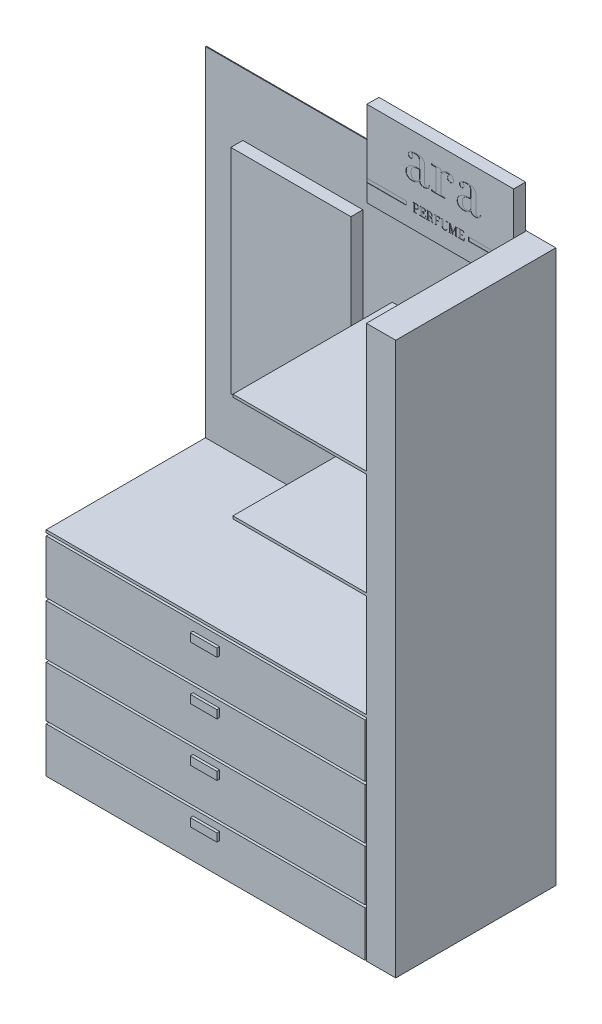
SolidWorks part; units mm, degrees
ref_plane "Front Plane" through (0, 0, 0) normal (0, 0, 1) x (1, 0, 0)
ref_plane "Top Plane" through (0, 0, 0) normal (0, 1, 0) x (1, 0, 0)
ref_plane "Right Plane" through (0, 0, 0) normal (1, 0, 0) x (0, 0, -1)
sketch "Sketch1" plane through (0, 0, 0) normal (0, 0, 1) x (1, 0, 0)
  line L1 (-655, 1035) -> (655, 1035)
  line L2 (-655, 1035) -> (-655, -1035)
  line L3 (-655, -1035) -> (655, -1035)
  line L4 (655, 1035) -> (655, -1035)
  line L5 (-655, 1035) -> (655, -1035) construction
  line L6 (-655, -1035) -> (655, 1035) construction
  point P0 (0, 0)
  dimension "D1" = 1310
  dimension "D2" = 2070
extrude "Boss-Extrude1" add sketch "Sketch1" along normal blind 600
sketch "Sketch2" plane through (0, 0, 600) normal (0, 0, 1) x (1, 0, 0)
  line L0 (-655, -1035) -> (655, -1035) construction
  line L1 (545, -235) -> (-655, -235)
  line L2 (545, -235) -> (545, 165)
  line L3 (545, 165) -> (-655, 165)
  line L4 (-655, -235) -> (-655, 165)
  line L6 (-655, 1035) -> (-655, -1035) construction
  dimension "D1" = 400
  dimension "D2" = 1200
  dimension "D3" = 800
extrude "Cut-Extrude2" cut sketch "Sketch2" against normal offset from surface (597 mm away) 3 up to face at (0, 0, 0)
sketch "Sketch5" plane through (0, 0, 600) normal (0, 0, 1) x (1, 0, 0)
  line L8 (545, -245) -> (-655, -245)
  line L9 (545, -245) -> (545, -255)
  line L10 (545, -255) -> (-655, -255)
  line L11 (-655, -245) -> (-655, -255)
  line L12 (-655, 1035) -> (-655, 165) construction
  line L13 (545, -235) -> (-655, -235) construction
  line L14 (655, -1035) -> (655, 1035) construction
  dimension "D1" = 10
  dimension "D2" = 10
  dimension "D3" = 110
extrude "Cut-Extrude5" cut sketch "Sketch5" against normal offset from surface (597 mm away) 3 up to face at (0, 0, 0)
sketch "Sketch6" plane through (0, 0, 600) normal (0, 0, 1) x (1, 0, 0)
  line L1 (545, -455) -> (-655, -455)
  line L2 (545, -455) -> (545, -465)
  line L3 (545, -465) -> (-655, -465)
  line L4 (-655, -455) -> (-655, -465)
  line L5 (-655, -255) -> (-655, -1035) construction
  line L6 (-655, -255) -> (545, -255) construction
  line L7 (655, -1035) -> (655, 1035) construction
  dimension "D1" = 10
  dimension "D2" = 200
  dimension "D3" = 110
extrude "Cut-Extrude6" cut sketch "Sketch6" against normal offset from surface (597 mm away) 3 up to face at (0, 0, 0)
pattern_linear "LPattern2" count 3 spacing 200 along (0, -1, 0) of "Cut-Extrude6"
sketch "Sketch9" plane through (0, 0, 600) normal (0, 0, 1) x (1, 0, 0)
  line L0 (545, -255) -> (-655, -255) construction
  line L1 (-105, -289.2371) -> (-5, -289.2371)
  line L2 (-105, -289.2371) -> (-105, -319.2371)
  line L3 (-105, -319.2371) -> (-5, -319.2371)
  line L4 (-5, -289.2371) -> (-5, -319.2371)
  point P6 (-55, -255)
  point P7 (-55, -289.2371)
  dimension "D1" = 100
  dimension "D2" = 30
extrude "Boss-Extrude2" add sketch "Sketch9" along normal blind 10
pattern_linear "LPattern3" count 4 spacing 200 along (0, -1, 0) of "Boss-Extrude2"
sketch "Sketch11" plane through (0, 0, 600) normal (0, 0, 1) x (1, 0, 0)
  line L0 (655, 1035) -> (-655, 1035) construction
  line L1 (655, -1035) -> (545, -1035)
  line L2 (655, -1035) -> (655, 1035)
  line L3 (655, 1035) -> (545, 1035)
  line L4 (545, -1035) -> (545, 1035)
  dimension "D1" = 110
extrude "Boss-Extrude3" add sketch "Sketch11" against normal up to surface (600 mm away) separate body up to face at (0, 0, 0)
sketch "Sketch12" plane through (0, 0, 600) normal (0, 0, 1) x (1, 0, 0)
  line L0 (545, 1035) -> (545, -1035) construction
  line L1 (545, 665) -> (45, 665)
  line L2 (545, 665) -> (545, 675)
  line L3 (545, 675) -> (45, 675)
  line L4 (45, 665) -> (45, 675)
  line L6 (545, 165) -> (-655, 165) construction
  dimension "D1" = 10
  dimension "D2" = 500
  dimension "D3" = 500
extrude "Cut-Extrude9" cut sketch "Sketch12" against normal offset from surface (597 mm away) 3 up to face at (0, 0, 0)
sketch "Sketch13" plane through (0, 0, 600) normal (0, 0, 1) x (1, 0, 0)
  line L1 (545, 165) -> (-655, 165)
  line L2 (545, 165) -> (545, 1035)
  line L3 (545, 1035) -> (-655, 1035)
  line L4 (-655, 165) -> (-655, 1035)
extrude "Cut-Extrude10" cut sketch "Sketch13" against normal offset from surface (597 mm away) 3 up to face at (0, 0, 0)
sketch "Sketch14" plane through (0, 0, 3) normal (0, 0, 1) x (1, 0, 0)
  line L0 (545, 1035) -> (545, -235) construction
  line L1 (545, 160) -> (45, 160)
  line L2 (545, 160) -> (545, 150)
  line L3 (545, 150) -> (45, 150)
  line L4 (45, 160) -> (45, 150)
  line L5 (545, -235) -> (-655, -235) construction
  dimension "D1" = 500
  dimension "D2" = 10
  dimension "D3" = 385
extrude "Boss-Extrude4" add sketch "Sketch14" along normal up to surface (597 mm away) up to face at (600, 0, 600)
pattern_linear "LPattern4" count 2 spacing 395 along (0, 1, 0) of "Boss-Extrude4"
sketch "Sketch16" plane through (0, 0, 600) normal (0, 0, 1) x (1, 0, 0)
  line L0 (-655, -1035) -> (655, -1035) construction
  line L1 (545, -255) -> (540, -255)
  line L2 (545, -255) -> (545, -1035)
  line L3 (545, -1035) -> (540, -1035)
  line L4 (540, -255) -> (540, -1035)
  dimension "D1" = 5
extrude "Cut-Extrude11" cut sketch "Sketch16" against normal offset from surface (597 mm away) 3 up to face at (0, 0, 0)
sketch "Sketch17" plane through (0, 0, 3) normal (0, 0, 1) x (1, 0, 0)
  line L1 (-515, 800) -> (-65, 800)
  line L2 (-515, 800) -> (-515, 0)
  line L3 (-515, 0) -> (-65, 0)
  line L4 (-65, 800) -> (-65, 0)
  line L5 (545, -235) -> (-655, -235) construction
  line L7 (-655, -235) -> (-655, 1035) construction
  dimension "D1" = 450
  dimension "D2" = 800
  dimension "D3" = 235
  dimension "D4" = 140
extrude "Boss-Extrude5" add sketch "Sketch17" along normal blind 45
sketch "Sketch18" plane through (0, 0, 3) normal (0, 0, 1) x (1, 0, 0)
  line L1 (545, 1195) -> (-5, 1195)
  line L2 (545, 1195) -> (545, 875)
  line L3 (545, 875) -> (-5, 875)
  line L4 (-5, 1195) -> (-5, 875)
  line L5 (-655, 1035) -> (545, 1035) construction
  line L6 (-655, -235) -> (-655, 1035) construction
  point P4 (-5, 1035)
  dimension "D1" = 320
  dimension "D2" = 550
  dimension "D3" = 650
extrude "Boss-Extrude6" add sketch "Sketch18" along normal blind 45
sketch "Sketch19" plane through (0, 0, 48) normal (0, 0, 1) x (1, 0, 0)
  text T0 "ara" font "BodoniFLF" height in points 500
extrude "Cut-Extrude12" cut sketch "Sketch19" against normal blind 1
sketch "Sketch21" plane through (0, 0, 48) normal (0, 0, 1) x (1, 0, 0)
  text T0 "PERFUME" font "BodoniFLF" height in points 100
extrude "Cut-Extrude13" cut sketch "Sketch21" against normal blind 1
sketch "Sketch22" plane through (0, 0, 48) normal (0, 0, 1) x (1, 0, 0)
  line L0 (-5, 1035) -> (-5, 875) construction
  line L1 (-5, 955) -> (143.6154, 955)
  line L2 (-5, 955) -> (-5, 940.9396)
  line L3 (-5, 940.9396) -> (143.6154, 940.9396)
  line L4 (143.6154, 955) -> (143.6154, 940.9396)
  line L5 (545, 1035) -> (545, 555) construction
  line L6 (376.5099, 955) -> (545, 955)
  line L7 (376.5099, 955) -> (376.5099, 940.9396)
  line L8 (376.5099, 940.9396) -> (545, 940.9396)
  line L9 (545, 955) -> (545, 940.9396)
extrude "Cut-Extrude14" cut sketch "Sketch22" against normal blind 1
